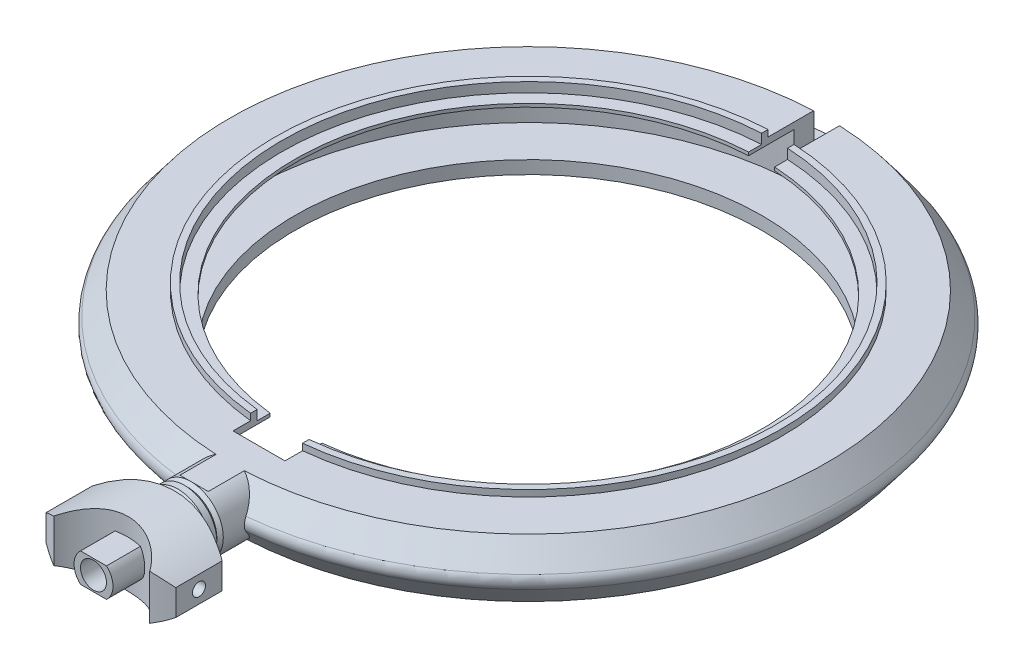
SolidWorks part; units mm, degrees
ref_plane "Alzado" through (0, 0, 0) normal (0, 0, 1) x (1, 0, 0)
ref_plane "Planta" through (0, 0, 0) normal (0, 1, 0) x (1, 0, 0)
ref_plane "Vista lateral" through (0, 0, 0) normal (1, 0, 0) x (0, 0, -1)
sketch "Croquis1" plane through (0, 0, 0) normal (0, 0, 1) x (1, 0, 0)
  line L0 (18, 0) -> (21, 0)
  line L1 (21, 0) -> (21, 0.5)
  line L2 (21, 0.5) -> (23, 0.5)
  line L3 (18, 0) -> (18, 1)
  line L4 (18, 1) -> (21.5, 1)
  line L5 (23, 5) -> (19.5, 5)
  line L6 (19.5, 5) -> (19.5, 5.5)
  line L7 (19.5, 5.5) -> (19, 5.5)
  line L8 (19, 5.5) -> (19, 4.75)
  line L9 (19, 4.75) -> (18, 4.75)
  line L10 (18, 4.75) -> (18, 4.5)
  line L11 (18, 4.5) -> (21.5, 4.5)
  line L12 (21.5, 4.5) -> (21.5, 1)
  line L14 (23, 5) -> (24.3314, 3.25)
  line L15 (23, 0.5) -> (24.3314, 2.25)
  line L16 (24.5, 2.75) -> (21.5, 2.75) construction
  line L17 (0, 0) -> (0, 4.9856) construction
  arc A0 (24.3314, 3.25) -> (24.3314, 2.25) centre (23.6742, 2.75) cw
  dimension "D1" = 18
  dimension "D2" = 21
  dimension "D3" = 0.5
  dimension "D4" = 1
  dimension "D5" = 1
  dimension "D6" = 3.5
  dimension "D7" = 4.5
  dimension "D8" = 0.5
  dimension "D9" = 0.25
  dimension "D10" = 1
  dimension "D11" = 0.5
  dimension "D12" = 24.5
  dimension "D13" = 1
  dimension "D14" = 3.5
revolve "Revolución1" add sketch "Croquis1" angle 360 about L17
sketch "Croquis2" plane through (0, 0, 0) normal (1, 0, 0) x (0, 0, -1)
  line L0 (23, 3) -> (23, 5)
  line L1 (23, 5) -> (24.5, 5)
  line L2 (24.5, 5) -> (24.5, 2.5)
  line L3 (24.5, 2.5) -> (23.5, 2.5)
  arc A0 (23, 3) -> (23.5, 2.5) centre (23.5, 3) ccw
  dimension "D2" = 0.5
  dimension "D1" = 23.5
  dimension "D3" = 2.5
  dimension "D4" = 1.5
  dimension "D5" = 2.5
extrude "Cortar-Extruir1" cut sketch "Croquis2" against normal through all and the other way through all
sketch "Croquis3" plane through (0, 0, 0) normal (0, -1, 0) x (1, 0, 0)
  line L0 (-2, 17.5) -> (-2, 20.75)
  line L1 (2, 17.5) -> (2, 20.75)
  line L2 (-2, 20.75) -> (2, 20.75)
  line L3 (-2, 17.5) -> (2, 17.5)
  circle A2 centre (0, 0) radius 18 construction
  dimension "D2" = 2
  dimension "D3" = 4
  dimension "D4" = 17.5
  dimension "D5" = 20.75
extrude "Cortar-Extruir2" cut sketch "Croquis3" against normal through all
sketch "Croquis5" plane through (0, 0, 0) normal (1, 0, 0) x (0, 0, -1)
  line L0 (-23, 0.5) -> (23, 0.5) construction
  line L7 (-22, 0.25) -> (-22, 2.75)
  line L10 (-26.5, 0.25) -> (-27, 0.25)
  line L11 (-28.5, 2.75) -> (-22, 2.75)
  line L12 (-26, 0.25) -> (-22, 0.25)
  line L13 (-26.25, 0.5) -> (-26, 0.25)
  line L14 (-26.5, 0.25) -> (-26.25, 0.5)
  line L15 (-28.5, 0.25) -> (-28.5, 2.75)
  line L16 (-27.5, 0.75) -> (-28, 0.25)
  line L17 (-27, 0.25) -> (-27.5, 0.75)
  line L18 (-28, 0.25) -> (-28.5, 0.25)
  dimension "D1" = 2.5
  dimension "D2" = 6.5
  dimension "D3" = 90
  dimension "D4" = 90
  dimension "D5" = 4
  dimension "D6" = 0.5
  dimension "D7" = 0.5
  dimension "D8" = 22
  dimension "D9" = 2.25
  dimension "D10" = 0.5
  dimension "D11" = 0.25
  dimension "D12" = 0.5
  dimension "D13" = 1
  dimension "D14" = 0.5
  dimension "D15" = 0.25
  dimension "D16" = 0.5
revolve "Revolución2" add sketch "Croquis5" angle 360 about L11
sketch "Croquis6" plane through (0, 0, 0) normal (1, 0, 0) x (0, 0, -1)
  line L0 (-28.5, 2.75) -> (-22, 2.75) construction
  line L2 (-28.5, 5.25) -> (-28.5, 0.25) construction
  line L3 (-22, 2.75) -> (-26, 2.75) construction
  line L4 (-28, 2.75) -> (-28.5, 2.75) construction
  line L5 (-22, 0) -> (-22, 0.5)
  line L7 (-22, 0.5) -> (-25.75, 0.5)
  line L8 (-22, 5) -> (-25.75, 5)
  line L9 (-26.25, 0) -> (-25.75, 0.5)
  line L10 (-28, 5.25) -> (-28.5, 4.75)
  line L11 (-28, 0.25) -> (-28.5, 0.75)
  line L12 (-28, 0.25) -> (-28.5, 0.25)
  line L13 (-28.5, 0.25) -> (-28.5, 0.75)
  line L14 (-28, 5.25) -> (-28.5, 5.25)
  line L15 (-28.5, 4.75) -> (-28.5, 5.25)
  line L16 (-26.25, 5.5) -> (-25.75, 5)
  line L17 (-26.25, 0) -> (-26.25, -0.75)
  line L18 (-26.25, -0.75) -> (-22, -0.75)
  line L19 (-22, -0.75) -> (-22, 0)
  line L20 (-26.25, 5.5) -> (-26.25, 6.25)
  line L21 (-22, 0.5) -> (-22.9742, 0.5) construction
  line L22 (-26.25, 6.25) -> (-22, 6.25)
  line L24 (-22, 6.25) -> (-22, 5.5)
  line L25 (-22, 5.5) -> (-22, 5)
  dimension "D2" = 3.75
  dimension "D3" = 1.25
  dimension "D5" = 45
  dimension "D6" = 45
  dimension "D8" = 4.25
  dimension "D9" = 135
extrude "Cortar-Extruir3" cut sketch "Croquis6" against normal through all and the other way through all
ref_plane "Plano1" through (0, 2.75, 0) normal (0, 1, 0) x (-1, 0, 0)
sketch "Croquis8" plane through (0, 2.75, 0) normal (0, 1, 0) x (-1, 0, 0)
  line L0 (0, 23.1181) -> (0, 26.9797) construction
  line L1 (1.5, 28.5) -> (-1.5, 28.5) construction
  arc A0 (-7.2618, 30.375) -> (7.2618, 30.375) centre (0, 37.25) ccw
  arc A1 (7.2618, 30.375) -> (-7.2618, 30.375) centre (0, 23.5) ccw
  dimension "D3" = 20
  dimension "D4" = 20
  dimension "D1" = 37.25
  dimension "D2" = 5
extrude "Saliente-Extruir1" add sketch "Croquis8" along normal blind 2.5 and the other way blind 2.5
sketch "Croquis9" plane through (0, 0, 0) normal (0, 1, 0) x (1, 0, 0)
  line L1 (5, -33) -> (8, -33)
  line L2 (5, -33) -> (5, -26)
  line L3 (5, -26) -> (8, -26)
  line L4 (8, -33) -> (8, -26)
  line L5 (-5, -33) -> (-8, -33)
  line L6 (-5, -33) -> (-5, -26)
  line L7 (-5, -26) -> (-8, -26)
  line L8 (-8, -33) -> (-8, -26)
  dimension "D1" = 7
  dimension "D2" = 3
  dimension "D3" = 5
  dimension "D4" = 5
  dimension "D5" = 26
extrude "Cortar-Extruir5" cut sketch "Croquis9" along normal through all
ref_plane "Plano2" through (0, 0, 33.5) normal (0, 0, 1) x (1, 0, 0)
sketch "Croquis10" plane through (0, 0, 33.5) normal (0, 0, 1) x (1, 0, 0)
  line L0 (-5, 3.75) -> (-5, 5.25)
  line L1 (-5, 0.25) -> (-5, 5.25) construction
  line L2 (-5, 5.25) -> (5, 5.25)
  line L3 (5, 5.25) -> (5, 3.75)
  line L4 (5, 5.25) -> (5, 0.25) construction
  line L5 (-5, 1.75) -> (-5, 0.25)
  line L6 (-5, 0.25) -> (5, 0.25)
  line L7 (5, 0.25) -> (5, 1.75)
  line L8 (0, 16.5938) -> (0, -24.9377) construction
  arc A0 (5, 3.75) -> (-5, 3.75) centre (0, -3.8333) ccw
  arc A1 (-5, 1.75) -> (5, 1.75) centre (0, 9.3333) ccw
  dimension "D1" = 1.5
  dimension "D2" = 1.5
extrude "Cortar-Extruir6" cut sketch "Croquis10" against normal blind 6.5 contours A0 L3 L2 | A0 L2 L0 | A1 L5 L6 | A1 L6 L7
sketch "Croquis12" plane through (0, 2.75, 0) normal (0, 1, 0) x (-1, 0, 0)
  line L0 (0, 27.9836) -> (0, 35.1578) construction
  arc A0 (5, 32.1603) -> (-5, 32.1603) centre (0, 23.5) ccw construction
  circle A1 centre (0.1131, 35.1986) radius 4.45
  point P0 (0, 33.5)
  point P1 (4, 33.0319)
  point P5 (-4, 33.5)
  point P6 (0, 30.75)
  dimension "D3" = 2.75
  dimension "D1" = 4
  dimension "D2" = 4
extrude "Cortar-Extruir7" cut sketch "Croquis12" against normal blind 6.5 and the other way blind 6.5
sketch "Croquis15" plane through (0, 0, 33.5) normal (0, 0, 1) x (1, 0, 0)
  line L0 (0, 1.9926) -> (0, 4.2647) construction
  line L1 (-1, 3.868) -> (1, 3.868)
  line L2 (-1, 1.632) -> (1, 1.632)
  arc A0 (-1, 3.868) -> (-1, 1.632) centre (0, 2.75) ccw
  arc A1 (1, 1.632) -> (1, 3.868) centre (0, 2.75) ccw
  point P4 (0, 1.632)
  point P5 (0, 3.868)
  dimension "D1" = 3
  dimension "D2" = 2.75
  dimension "D4" = 2
extrude "Saliente-Extruir2" add sketch "Croquis15" against normal up to surface (2.61 mm away)
sketch "Croquis13" plane through (0, 0, 0) normal (0, 0, 1) x (1, 0, 0)
  circle A0 centre (0, 2.75) radius 1
  dimension "D1" = 2
  dimension "D2" = 2.75
extrude "Cortar-Extruir8" cut sketch "Croquis13" along normal through all
hole_wizard "Diámetro de taladro Ø1.0 (1)1" positions "Croquis3D1" profile "Croquis14" hole size "Ø1.0" standard "ISO"
sketch3d "Croquis3D1"
  line L0 (-5, 3.75, 28.5897) -> (-5, 3.75, 32.1603) construction
  line L1 (-5, 3.75, 28.5897) -> (-5, 1.75, 28.5897) construction
  line L2 (5, 3.75, 32.1603) -> (5, 3.75, 28.5897) construction
  line L3 (5, 1.75, 28.5897) -> (5, 3.75, 28.5897) construction
  point P0 (5, 2.75, 30.375)
  point P2 (-5, 2.75, 30.375)
  point P8 (-5, 3.75, 30.375)
  point P11 (-5, 2.75, 28.5897)
  point P15 (5, 3.75, 30.375)
  point P18 (5, 2.75, 28.5897)
sketch "Croquis14" plane through (5, 2.75, 30.375) normal (0, 1, 0) x (0, 0, -1)
  line L0 (0, 0) -> (0, 2.3004)
  line L1 (0, 2.3004) -> (0.5, 2)
  line L2 (0.5, 2) -> (0.5, 0)
  line L5 (0.5, 0) -> (0, 0)
  line L10 (0, 2.3004) -> (-0.5, 2) construction
  line L11 (0, -6.35) -> (0, 107.95) construction
  dimension "Diámetro de taladro" = 1
  dimension "Profundidad de taladro" = 2
  dimension "Ángulo de perforador" = 118
sketch "Croquis16" plane through (0, 5.5, 0) normal (0, 1, 0) x (1, 0, 0)
  line L0 (-8.3278, 23) -> (8.3278, 23) construction
  line L1 (-1, 23) -> (1, 23)
  line L2 (-1, 23) -> (-1, 16)
  line L3 (-1, 16) -> (1, 16)
  line L4 (1, 23) -> (1, 16)
  point P6 (0, 23)
  dimension "D1" = 2
  dimension "D2" = 7
extrude "Cortar-Extruir9" cut sketch "Croquis16" against normal up to vertex
